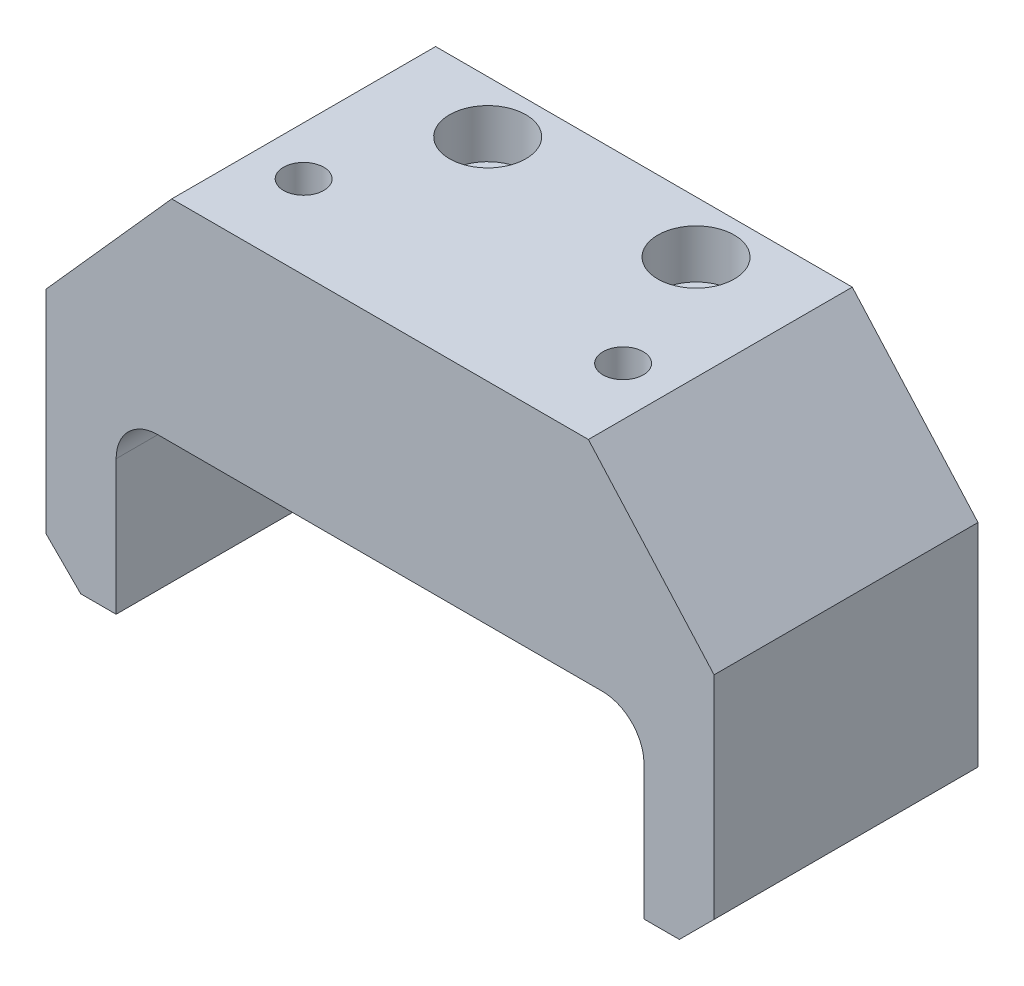
SolidWorks part; units mm, degrees
material "PET"
ref_plane "Front Plane" through (0, 0, 0) normal (0, 0, 1) x (1, 0, 0)
ref_plane "Top Plane" through (0, 0, 0) normal (0, 1, 0) x (1, 0, 0)
ref_plane "Right Plane" through (0, 0, 0) normal (1, 0, 0) x (0, 0, -1)
sketch "Sketch1" plane through (0, 0, 0) normal (0, 0, 1) x (1, 0, 0)
  line L0 (0, 19.0297) -> (0, -2.5925) construction
  line L1 (-12.9623, 0) -> (13.1829, 0) construction
  line L2 (48.1, 6) -> (-48.1, 6)
  line L3 (-48.1, 6) -> (-48.1, -49.8)
  line L4 (-48.1, -49.8) -> (-38, -49.8)
  line L5 (-38, -49.8) -> (-38, -24.4)
  line L6 (-38, -24.4) -> (38, -24.4)
  line L7 (48.1, -49.8) -> (38, -49.8)
  line L8 (38, -49.8) -> (38, -24.4)
  line L9 (48.1, 6) -> (48.1, -49.8)
  circle A0 centre (0, 0) radius 3.75 construction
  point P16 (0, -24.4)
  point P17 (0, 6)
  dimension "D1" = 7.5
  dimension "D2" = 6
  dimension "D6" = 24.4
  dimension "D3" = 96.2
  dimension "D4" = 25.4
  dimension "D5" = 76
extrude "Boss-Extrude1" add sketch "Sketch1" along normal mid plane 38
sketch "Sketch9" plane through (0, 0, 19) normal (0, 0, 1) x (1, 0, 0)
  line L0 (0, 0) -> (0, -24.4) construction
  line L1 (-38, -24.4) -> (38, -24.4) construction
  line L2 (-30, 6) -> (-48.1, -14.3)
  line L3 (48.1, 6) -> (-48.1, 6) construction
  line L4 (-48.1, 6) -> (-48.1, -49.8) construction
  line L5 (-48.1, -14.3) -> (-48.1, 6)
  line L6 (-48.1, 6) -> (-30, 6)
  line L7 (-38, -24.4) -> (-48.1, -24.4) construction
  line L8 (-48.1, -24.4) -> (-48.1, -14.3) construction
  line L9 (48.1, 6) -> (30, 6)
  line L10 (48.1, -14.3) -> (48.1, 6)
  line L11 (30, 6) -> (48.1, -14.3)
  dimension "D1" = 30
extrude "Cut-Extrude8" cut sketch "Sketch9" against normal through all
fillet "Fillet1" radius 6 2 edges at (38, -24.4, 0) (-38, -24.4, 0)
sketch "Sketch2" plane through (0, 6, 0) normal (0, 1, 0) x (1, 0, 0)
  line L0 (0, 35.9356) -> (0, 6.1551) construction
  line L3 (30, 19) -> (-30, 19) construction
  circle A4 centre (-15, 11.5) radius 3.05
  circle A7 centre (15, 11.5) radius 3.05
  dimension "D4" = 6.1
  dimension "D9" = 7.5
  dimension "D10" = 15
extrude "Cut-Extrude1" cut sketch "Sketch2" against normal blind 42
sketch "Sketch3" plane through (0, 6, 0) normal (0, 1, 0) x (1, 0, 0)
  circle A0 centre (-15, 11.5) radius 5.5
  circle A1 centre (15, 11.5) radius 5.5
  dimension "D1" = 11
extrude "Cut-Extrude2" cut sketch "Sketch3" against normal blind 7
sketch "Sketch8" plane through (0, 6, 0) normal (0, 1, 0) x (1, 0, 0)
  line L0 (-23, -7) -> (0, -7) construction
  line L1 (0, -7) -> (0, 0) construction
  line L2 (30, -19) -> (-30, -19) construction
  circle A0 centre (-23, -7) radius 2.9
  circle A1 centre (23, -7) radius 2.9
  dimension "D1" = 5.8
  dimension "D2" = 46
  dimension "D3" = 12
extrude "Cut-Extrude7" cut sketch "Sketch8" against normal blind 23
chamfer "Chamfer2" distance 5 angle 45 2 edges at (48.1, -49.8, 0) (-48.1, -49.8, 0)
equation "\"M5_tap\"=4.2mm\t\t\t\t\t\t\t' Below you can do mesurements as follows: cm, mm, ft, in, m, "
equation "\"M5_clearence\"=5.5mm"
equation "\"M6_tap\"=5mm"
equation "\"M6_clearence\"=6.6mm"
equation "\"work_area_width\"=1100mm"
equation "\"work_area_depth\"=900mm"
equation "\"steel_base_width\"=3in\t"
equation "\"steel_base_height\"=2in"
equation "\"steel_base_wall_thickness\"=0.125in"
equation "\"steel_base_radius\"=6mm"
equation "\"steel_sides_width\"=3in\t\t\t\t\t'this tube is rotated so flip width/height"
equation "\"steel_sides_height\"=2in\t\t\t\t'this tube is rotated so flip width/height"
equation "\"steel_sides_wall_thickness\"=0.125in"
equation "\"steel_sides_radius\"=6mm"
equation "\"steel_gantry_width\"=4in\t\t\t\t'this tube is rotated so flip width/height"
equation "\"steel_gantry_height\"=3in\t\t\t\t'this tube is rotated so flip width/height"
equation "\"steel_gantry_wall_thickness\"=0.125in"
equation "\"steel_gantry_radius\"=6mm"
equation "\"steel_rollers_width\"=3in"
equation "\"steel_rollers_height\"=2in\t\t\t\t'keep as low as possible as this increases how big plastic parts are"
equation "\"steel_rollers_wall_thickness\"=0.125in"
equation "\"steel_rollers_radius\"=6mm"
equation "\"steel_zbox_width\"=4in\t\t\t\t\t'if the gantry height (rotated) is too thick, a wider zbox is necessary"
equation "\"steel_zbox_height\"=2in\t\t\t\t\t'hole patteren changes as the zbox and gantry height (rotated) changes."
equation "\"steel_zbox_wall_thickness\"=0.125in"
equation "\"steel_zbox_radius\"=6mm"
equation "\"alu_zangle_width\"=4in\t\t\t\t\t'check that it doesn't interfer with the gantry"
equation "\"alu_zangle_height\"=4in"
equation "\"alu_zangle_wall_thickness\"=0.375in\t\t\t'check that it doesn't interfer with the gantry"
equation "\"D6@Sketch1\"=\"steel_zbox_height\" /2 -1"
equation "\"D4@Sketch1\"=\"steel_rollers_width\"/3"
equation "\"D3@Sketch1\"=\"steel_gantry_height\" + 20mm"
